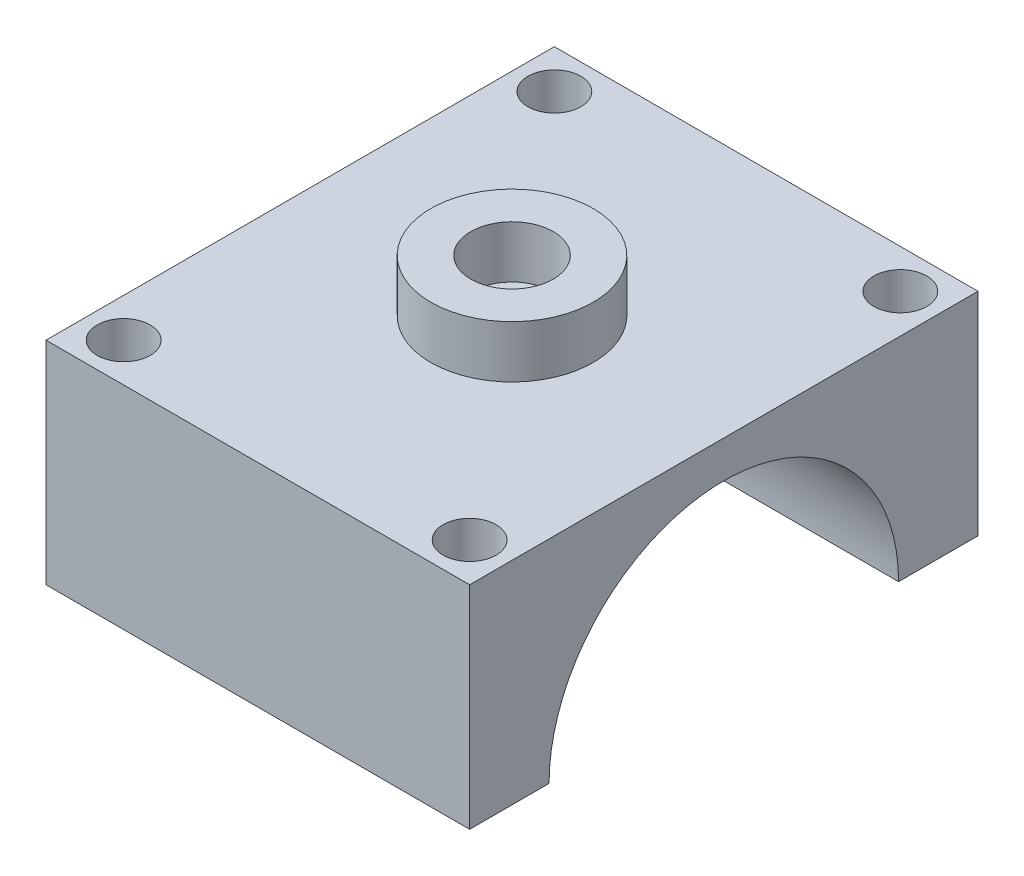
SolidWorks part; units mm, degrees
ref_plane "Front Plane" through (0, 0, 0) normal (0, 0, 1) x (1, 0, 0)
ref_plane "Top Plane" through (0, 0, 0) normal (0, 1, 0) x (1, 0, 0)
ref_plane "Right Plane" through (0, 0, 0) normal (1, 0, 0) x (0, 0, -1)
sketch "Sketch1" plane through (0, 0, 0) normal (0, 1, 0) x (1, 0, 0)
  line L1 (-15, -18) -> (15, -18)
  line L2 (-15, -18) -> (-15, 18)
  line L3 (-15, 18) -> (15, 18)
  line L4 (15, -18) -> (15, 18)
  line L5 (-15, -18) -> (15, 18) construction
  line L6 (-15, 18) -> (15, -18) construction
  point P0 (0, 0)
  dimension "D1" = 30
  dimension "D2" = 36
extrude "Boss-Extrude1" add sketch "Sketch1" along normal blind 30
sketch "Sketch3" plane through (15, 0, 0) normal (1, 0, 0) x (0, 0, -1)
  line L0 (0, 0) -> (0, 30) construction
  line L1 (-18, 0) -> (18, 0) construction
  line L2 (-18, 30) -> (18, 30) construction
  circle A0 centre (0, 15) radius 12.375
  dimension "D1" = 24.75
extrude "Cut-Extrude1" cut sketch "Sketch3" against normal blind 40
sketch "Sketch5" plane through (0, 30, 0) normal (0, 1, 0) x (1, 0, 0)
  line L7 (15, 18) -> (-15, 18) construction
  line L9 (-15, 18) -> (-15, -18) construction
  line L10 (0, 0) -> (0, 2.7791) construction
  line L11 (0, 2.7791) -> (0, 0) construction
  line L12 (0, 0) -> (-2.7536, 0) construction
  circle A1 centre (-12.25, 15.25) radius 1.875
  circle A2 centre (-12.25, -15.25) radius 1.875
  circle A3 centre (12.25, -15.25) radius 1.875
  circle A4 centre (12.25, 15.25) radius 1.875
  point P0 (0, 0)
  dimension "D2" = 3.75
  dimension "D3" = 2.75
  dimension "D4" = 2.75
extrude "Cut-Extrude2" cut sketch "Sketch5" against normal blind 40
sketch "Sketch7" plane through (0, 0, 0) normal (1, 0, 0) x (0, 0, -1)
  line L0 (-18, 30) -> (-18, 0) construction
  line L1 (-18, 15) -> (18, 15)
  line L2 (-18, 15) -> (-18, 0)
  line L3 (-18, 0) -> (18, 0)
  line L4 (18, 15) -> (18, 0)
extrude "Cut-Extrude3" cut sketch "Sketch7" against normal through all from surface at 15 starting at face at (15, 15, -12.375)
sketch "Sketch8" plane through (0, 30, 0) normal (0, 1, 0) x (1, 0, 0)
  circle A0 centre (0, 0) radius 5.75
  dimension "D1" = 11.5
extrude "Boss-Extrude2" add sketch "Sketch8" along normal blind 3.7
ref_plane "Plane1" through (0, 30, 0) normal (0, 1, 0) x (1, 0, 0)
sketch "Sketch11" plane through (0, 33.7, 0) normal (0, 1, 0) x (1, 0, 0)
  circle A0 centre (0, 0) radius 2.92
  dimension "D1" = 5.84
extrude "Cut-Extrude5" cut sketch "Sketch11" against normal blind 3.7
sketch "Sketch12" plane through (0, 30, 0) normal (0, 1, 0) x (1, 0, 0)
  circle A0 centre (0, 0) radius 1.75
  dimension "D1" = 3.5
extrude "Cut-Extrude6" cut sketch "Sketch12" against normal blind 3.7
sketch "Sketch14" plane through (0, 15, 0) normal (0, -1, 0) x (1, 0, 0)
  circle A0 centre (0, 0) radius 2.55
  dimension "D1" = 5.1
extrude "Cut-Extrude8" cut sketch "Sketch14" against normal blind 13.5
